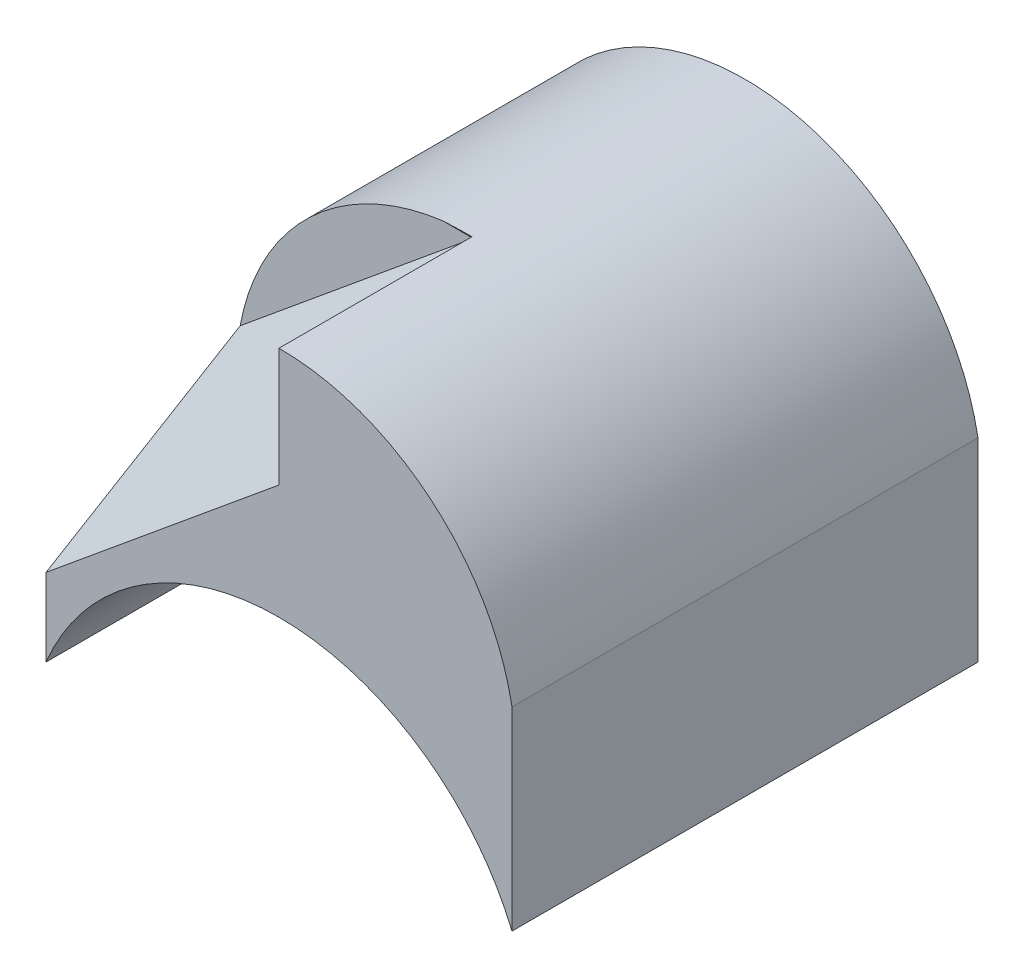
SolidWorks part; units mm, degrees
ref_plane "Front" through (0, 0, 0) normal (0, 0, 1) x (1, 0, 0)
ref_plane "Top" through (0, 0, 0) normal (0, 1, 0) x (1, 0, 0)
ref_plane "Right" through (0, 0, 0) normal (1, 0, 0) x (0, 0, -1)
sketch "Sketch1" plane through (0, 0, 0) normal (0, 1, 0) x (1, 0, 0)
  line L1 (-3, -3) -> (3, -3)
  line L2 (-3, -3) -> (-3, 3)
  line L3 (-3, 3) -> (3, 3)
  line L4 (3, -3) -> (3, 3)
  line L5 (-3, -3) -> (3, 3) construction
  line L6 (-3, 3) -> (3, -3) construction
  point P0 (0, 0)
  dimension "D1" = 6
  dimension "D2" = 6
extrude "Boss-Extrude1" add sketch "Sketch1" along normal blind 5
sketch "Sketch5" plane through (0, 0, 3) normal (0, 0, 1) x (1, 0, 0)
  line L0 (-3, 5) -> (-3, 0) construction
  line L1 (3, 5) -> (3, 0) construction
  line L6 (-3, 0) -> (3, 0)
  line L7 (3, 0) -> (3, 5)
  line L8 (3, 5) -> (-3, 5)
  line L9 (-3, 5) -> (-3, 0)
  line L10 (-3, 0) -> (3, 0)
  line L11 (3, 0) -> (3, 5)
  line L12 (3, 5) -> (-3, 5)
  line L13 (-3, 5) -> (-3, 0)
  arc A0 (-3, 0) -> (3, 0) centre (0, -1.25) cw
  arc A1 (-3, 2.5) -> (3, 2.5) centre (0, 1.95) cw
  point P8 (0, 2)
  point P14 (0, 5)
  line M5 (-3, 0) -> (3, 0)
  line M7 (3, 5) -> (-3, 5)
  line M8 (-3, 5) -> (-3, 0)
  dimension "D1" = 2
  dimension "D2" = 5
  dimension "D3" = 0
extrude "Cut-Extrude4" cut sketch "Sketch5" against normal blind 12.5 contours A1 L12 M8 | A1 L11 M7 | A0 M5
sketch3d "3DSketch1"
  line L0 (-3, 1, 3) -> (-3, 2.5, 0.5)
  line L1 (-3, 2.5, 3) -> (-3, 0, 3) construction
  line L2 (-3, 2.5, -3) -> (-3, 2.5, 3) construction
  line L3 (-3, 2.5, 0.5) -> (0, 4.9749, 0.5)
  line L4 (0, 4.9749, 0.5) -> (0, 3.4749, 3)
  line L5 (0, 3.4749, 3) -> (-3, 1, 3)
  dimension "D1" = 1
  dimension "D2" = 3
  dimension "D3" = 0
  dimension "D4" = 3
  dimension "D5" = 5
  dimension "D6" = 2.5
extrude "Cut-Extrude5" cut sketch "3DSketch1" along direction (1, 0, 0) on the side against the normal blind 10 contours L0 L3 L4 L5
sketch "Sketch7" plane through (0, 3.8786, 2.3272) normal (0, -0.8575, -0.5145) x (1, 0, 0)
  line L3 (-0.3902, -2.1308) -> (0, -2.1308)
  line L4 (0, -2.1308) -> (0, 0.7846)
  line L5 (0, 0.7846) -> (-2.6414, 0.7846)
  line L6 (-0.3902, -2.1308) -> (0, -2.1308)
  line L7 (0, -2.1308) -> (0, 0.7846)
  line L8 (0, 0.7846) -> (-2.6414, 0.7846)
  ellipse E1 centre (0, 3.7486) end of major axis (0, 9.6767) minor radius 3.05 (-2.6414, 0.7846) -> (-0.3902, -2.1308) ccw
  ellipse E2 centre (0, 3.7486) end of major axis (0, 9.6767) minor radius 3.05 (-2.6414, 0.7846) -> (-0.3902, -2.1308) ccw
  dimension "D1" = 0
extrude "Cut-Extrude6" cut sketch "Sketch7" against normal blind 10
